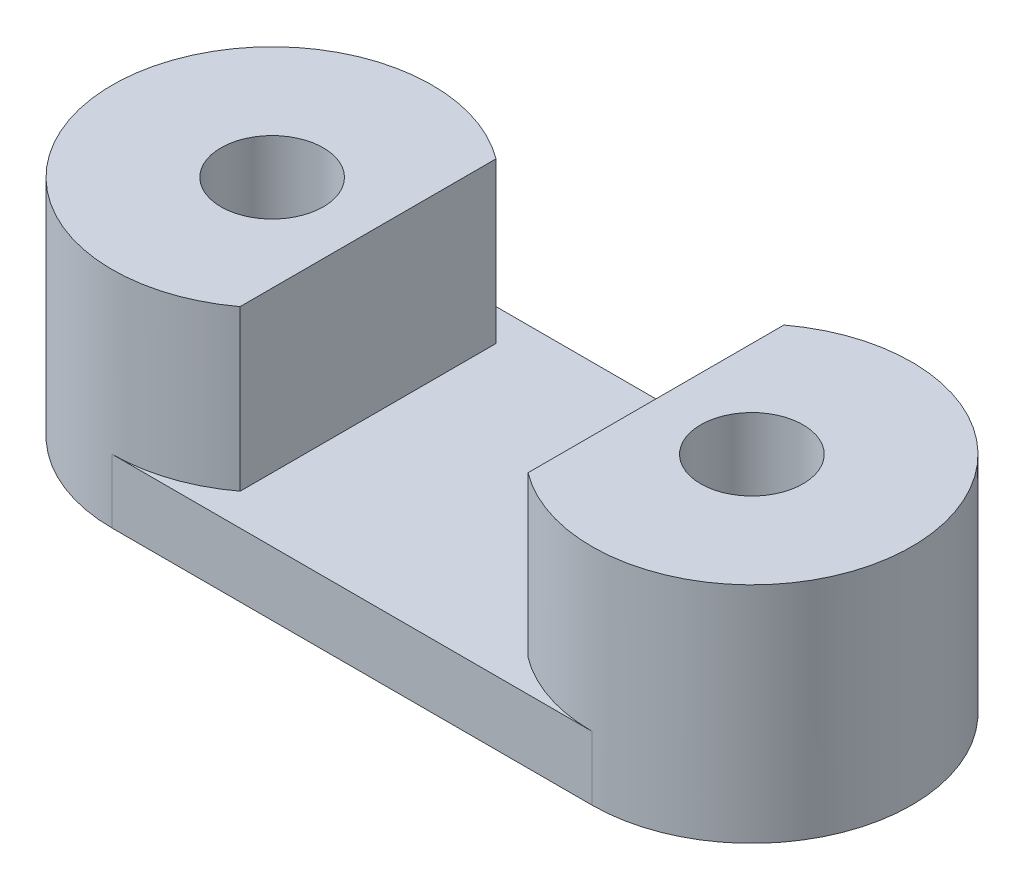
SolidWorks part; units mm, degrees
ref_plane "Front Plane" through (0, 0, 0) normal (0, 0, 1) x (1, 0, 0)
ref_plane "Top Plane" through (0, 0, 0) normal (0, 1, 0) x (1, 0, 0)
ref_plane "Right Plane" through (0, 0, 0) normal (1, 0, 0) x (0, 0, -1)
sketch "Sketch1" plane through (0, 0, 0) normal (0, 1, 0) x (1, 0, 0)
  line L0 (-7.5, 0) -> (7.5, 0) construction
  line L1 (-7.5, 5) -> (7.5, 5)
  line L2 (-7.5, -5) -> (7.5, -5)
  line L3 (-12.5, 0) -> (-12.5, 5) construction
  line L4 (-12.5, 5) -> (-7.5, 5) construction
  line L5 (12.5, 0) -> (12.5, 5) construction
  line L6 (12.5, 5) -> (7.5, 5) construction
  arc A0 (-7.5, 5) -> (-7.5, -5) centre (-7.5, 0) ccw
  arc A1 (7.5, -5) -> (7.5, 5) centre (7.5, 0) ccw
  circle A2 centre (-7.5, 0) radius 1.6
  circle A3 centre (7.5, 0) radius 1.6
  point P2 (0, 0)
  dimension "D2" = 25
  dimension "D3" = 3.2
  dimension "D4" = 3.2
  dimension "D1" = 10
extrude "Boss-Extrude1" add sketch "Sketch1" along normal blind 2
sketch "Sketch2" plane through (0, 2, 0) normal (0, 1, 0) x (1, 0, 0)
  circle A0 centre (-7.5, 0) radius 1.6
  circle A1 centre (-7.5, 0) radius 5
  circle A2 centre (7.5, 0) radius 1.6
  circle A3 centre (7.5, 0) radius 5
  arc A4 (-7.5, 5) -> (-7.5, -5) centre (-7.5, 0) ccw construction
  circle A5 centre (-7.5, 0) radius 1.6 construction
  circle A6 centre (7.5, 0) radius 1.6 construction
  arc A7 (7.5, -5) -> (7.5, 5) centre (7.5, 0) ccw construction
  dimension "D1" = 0
  dimension "D2" = 0
  dimension "D3" = 0
  dimension "D4" = 0
extrude "Boss-Extrude2" add sketch "Sketch2" along normal blind 5
sketch "Sketch3" plane through (0, 0, 5) normal (0, 0, 1) x (1, 0, 0)
  line L0 (-7.5, 2) -> (7.5, 2) construction
  line L1 (-4.5, 2) -> (4.5, 2)
  line L2 (-4.5, 2) -> (-4.5, 7)
  line L3 (-4.5, 7) -> (4.5, 7)
  line L4 (4.5, 2) -> (4.5, 7)
  line L5 (12.5, 7) -> (2.5, 7) construction
  line L6 (-2.5, 2) -> (-2.5, 7) construction
  line L7 (2.5, 7) -> (2.5, 2) construction
  dimension "D1" = 2
  dimension "D2" = 2
extrude "Cut-Extrude1" cut sketch "Sketch3" against normal through all
